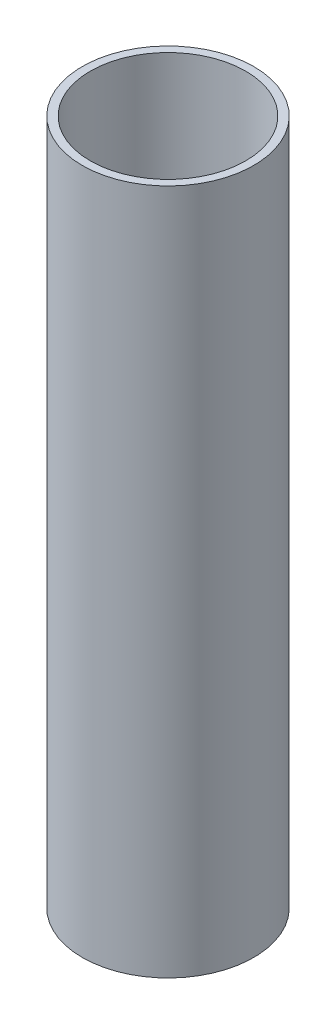
SolidWorks part; units mm, degrees
material "Thornel Mat VMA"
ref_plane "Front" through (0, 0, 0) normal (0, 0, 1) x (1, 0, 0)
ref_plane "Top" through (0, 0, 0) normal (0, 1, 0) x (1, 0, 0)
ref_plane "Right" through (0, 0, 0) normal (1, 0, 0) x (0, 0, -1)
sketch "Sketch1" plane through (0, 0, 0) normal (0, 1, 0) x (1, 0, 0)
  circle A0 centre (0, 0) radius 8.636
  circle A1 centre (0, 0) radius 9.525
  dimension "D1" = 19.05
  dimension "D2" = 17.272
extrude "Boss-Extrude1" add sketch "Sketch1" along normal mid plane 76.2
